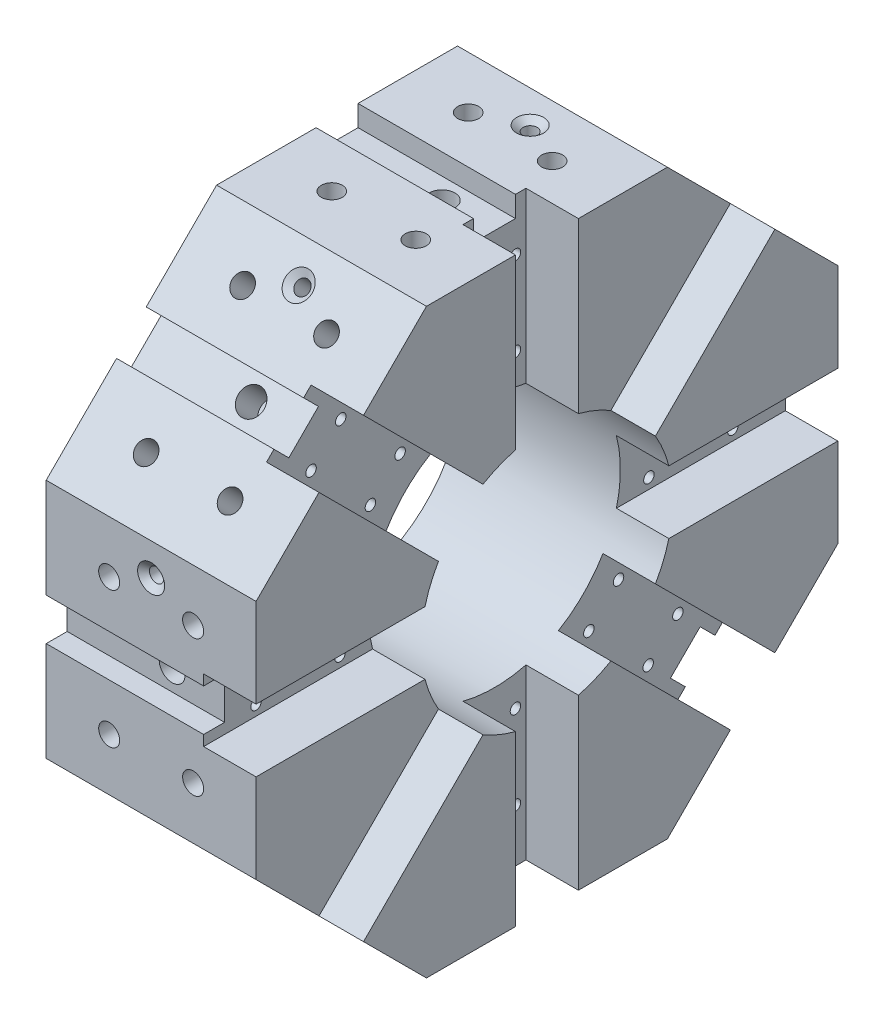
SolidWorks part; units mm, degrees
ref_plane "前视基准面" through (0, 0, 0) normal (0, 0, 1) x (1, 0, 0)
ref_plane "上视基准面" through (0, 0, 0) normal (0, 1, 0) x (1, 0, 0)
ref_plane "右视基准面" through (0, 0, 0) normal (1, 0, 0) x (0, 0, -1)
sketch "草图2" plane through (0, 0, 0) normal (1, 0, 0) x (0, 0, -1)
  line L0 (0, 0) -> (0, 167.4387) construction
  line L1 (-57.4025, 138.5819) -> (-138.5819, 57.4025)
  line L2 (-138.5819, 57.4025) -> (-138.5819, -57.4025)
  line L3 (-138.5819, -57.4025) -> (-57.4025, -138.5819)
  line L4 (-57.4025, -138.5819) -> (57.4025, -138.5819)
  line L5 (57.4025, -138.5819) -> (138.5819, -57.4025)
  line L6 (138.5819, -57.4025) -> (138.5819, 57.4025)
  line L7 (138.5819, 57.4025) -> (57.4025, 138.5819)
  line L8 (57.4025, 138.5819) -> (-57.4025, 138.5819)
  circle A0 centre (0, 0) radius 150 construction
  circle A1 centre (0, 0) radius 60
  dimension "D1" = 300
  dimension "D2" = 120
extrude "凸台-拉伸1" add sketch "草图2" along normal blind 100
sketch "草图4" plane through (0, 138.5819, 0) normal (0, 1, 0) x (1, 0, 0)
  line L0 (0, 0) -> (176.2457, 0) construction
  line L1 (100, 57.4025) -> (100, -57.4025) construction
  line L2 (100, 15) -> (75, 15)
  line L3 (100, 15) -> (100, -15)
  line L4 (100, -15) -> (75, -15)
  line L5 (75, 15) -> (75, -15)
  dimension "D1" = 25
  dimension "D2" = 30
  dimension "D3" = 15
extrude "切除-拉伸1" cut sketch "草图4" against normal up to next
sketch "草图6" plane through (75, 0, 0) normal (1, 0, 0) x (0, 0, -1)
  line L0 (0, 0) -> (0, 147.8627) construction
  line L1 (15, 138.5819) -> (-15, 138.5819) construction
  line L2 (-10, 138.5819) -> (10, 138.5819)
  line L3 (-10, 138.5819) -> (-10, 128.5819)
  line L4 (-10, 128.5819) -> (10, 128.5819)
  line L5 (10, 138.5819) -> (10, 128.5819)
  dimension "D1" = 20
  dimension "D2" = 10
  dimension "D3" = 10
extrude "切除-拉伸2" cut sketch "草图6" against normal up to next (75 mm away)
sketch "草图7" plane through (0, 138.5819, 0) normal (0, 1, 0) x (1, 0, 0)
  line L0 (50, 145.7401) -> (50, -155.8726) construction
  line L1 (-25.8561, 0) -> (127.2147, 0) construction
  circle A0 centre (30, 32.5) radius 5
  circle A1 centre (70, 32.5) radius 5
  circle A2 centre (30, -32.5) radius 5
  circle A3 centre (70, -32.5) radius 5
  dimension "D1" = 10
  dimension "D2" = 40
  dimension "D3" = 65
  dimension "D4" = 50
extrude "切除-拉伸3" cut sketch "草图7" against normal blind 20
hole_wizard "9/16-12 螺纹孔1" positions "草图9" profile "草图8" tap size "9/16-12" standard "Ansi Inch"
sketch "草图9" plane through (0, 128.5819, 0) normal (0, 1, 0) x (1, 0, 0)
  line L0 (0, 0) -> (92.2628, 0) construction
  line L1 (0, 10) -> (0, -10) construction
  line L3 (50, -15.0596) -> (50, 18.1793) construction
  point P0 (50, 0)
  dimension "D1" = 50
sketch "草图8" plane through (50, 128.5819, 0) normal (1, 0, 0) x (0, 0, 1)
  line L0 (0, 0) -> (0, 18.5518)
  line L1 (0, 18.5518) -> (6.1519, 15)
  line L2 (6.1519, 15) -> (6.1519, 0)
  line L5 (6.1519, 0) -> (0, 0)
  line L10 (0, 18.5518) -> (-6.1519, 15) construction
  line L11 (0, -6.35) -> (0, 107.95) construction
  dimension "螺纹孔钻头直径" = 12.3038
  dimension "螺纹孔钻头深度" = 15
  dimension "导头角度" = 120
cosmetic thread "孔螺蚊线1" parameters "D1"=15, "D2"=14.2875
sketch "草图10" plane through (75, 0, 0) normal (1, 0, 0) x (0, 0, -1)
  line L0 (-15, 58.0948) -> (-15, 138.5819) construction
  line L1 (-10, 138.5819) -> (-15, 138.5819) construction
  line L2 (15, 58.0948) -> (15, 138.5819) construction
  circle A0 centre (-10, 113.5819) radius 2.5
  circle A1 centre (10, 113.5819) radius 2.5
  circle A2 centre (10, 73.5819) radius 2.5
  circle A3 centre (-10, 73.5819) radius 2.5
  dimension "D2" = 5
  dimension "D1" = 5
  dimension "D3" = 25
  dimension "D4" = 2
  dimension "D6" = 5
  dimension "D5" = 2
extrude "切除-拉伸4" cut sketch "草图10" against normal blind 10
hole_wizard "1/4 平头机械螺钉的锥形沉头孔 (100)1" positions "草图14" profile "草图13" countersink size "1/4" standard "Ansi Inch"
sketch "草图14" plane through (0, 138.5819, 0) normal (0, 1, 0) x (1, 0, 0)
  line L0 (0, 10) -> (0, -10) construction
  point P0 (50, 42)
  point P3 (0, 0)
  point P6 (0, 0)
  dimension "D1" = 50
  dimension "D2" = 42
sketch "草图13" plane through (50, 138.5819, -42) normal (1, 0, 0) x (0, 0, 1)
  line L0 (0, 0) -> (0, 22.0298)
  line L1 (0, 22.0298) -> (3.3782, 20)
  line L2 (3.3782, 20) -> (3.3782, 2.5682)
  line L3 (3.3782, 2.5682) -> (6.4389, 0)
  line L5 (6.4389, 0) -> (0, 0)
  line L6 (-3.3782, 2.5682) -> (-6.4389, 0) construction
  line L10 (0, 22.0298) -> (-3.3782, 20) construction
  line L11 (0, -6.35) -> (0, 107.95) construction
  dimension "孔直径" = 6.7564
  dimension "孔深度" = 20
  dimension "近端锥形沉头孔直径" = 12.8778
  dimension "近端锥形沉头孔角度" = 100
  dimension "导头角度" = 118
pattern_circular "阵列(圆周)1" count 8 over 360 about axis through (0, 0, 0) along (1, 0, 0) of "切除-拉伸1", "切除-拉伸2", "切除-拉伸3", "9/16-12 螺纹孔1", "切除-拉伸4", "1/4 平头机械螺钉的锥形沉头孔 (100)1"
